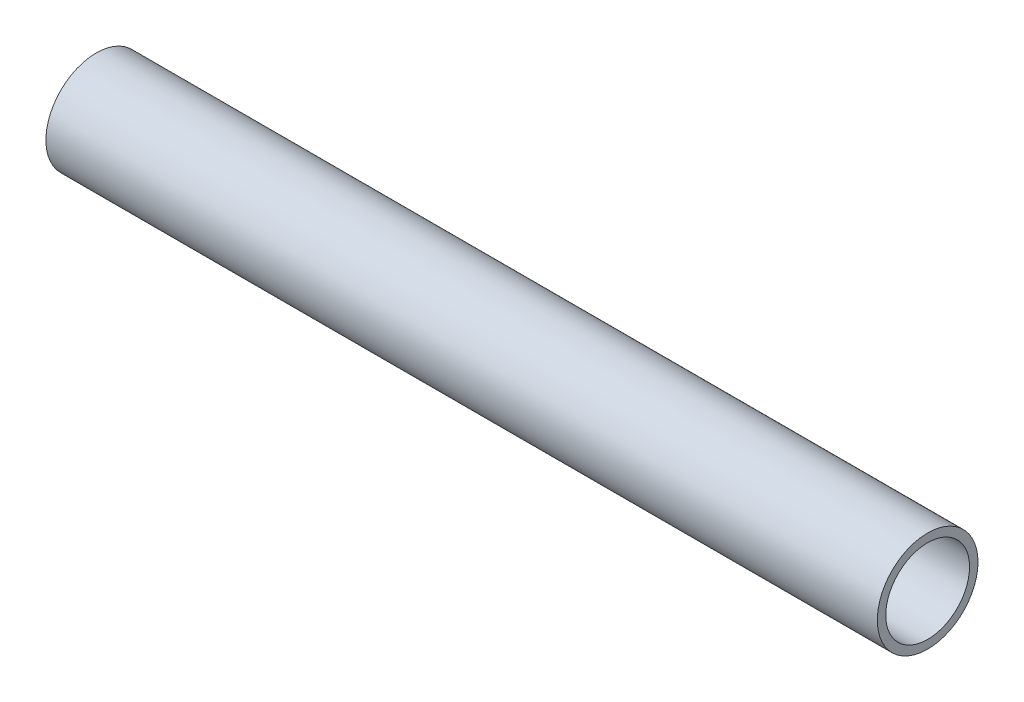
SolidWorks part; units mm, degrees
ref_plane "Front Plane" through (0, 0, 0) normal (0, 0, 1) x (1, 0, 0)
ref_plane "Top Plane" through (0, 0, 0) normal (0, 1, 0) x (1, 0, 0)
ref_plane "Right Plane" through (0, 0, 0) normal (1, 0, 0) x (0, 0, -1)
sketch "Sketch1" plane through (0, 0, 0) normal (0, 0, 1) x (1, 0, 0)
  line L0 (-143.6139, 1471.8597) -> (-38.7684, 1471.8597)
  point P2 (0, 0)
  point P3 (-143.6139, 1471.8597)
  point P5 (0, 0)
  point P6 (-144.5855, 1471.8597)
other "Pipe 0.5 SCH 40(1)"
ref_plane "Plane1" through (-143.6139, 1471.8597, 0) normal (1, 0, 0) x (0, 1, 0)
sketch "Sketch11" plane through (-143.6139, 1471.8597, 0) normal (1, 0, 0) x (0, 1, 0)
  circle A0 centre (0, 0) radius 5.2832
  circle A1 centre (0, 0) radius 6.35
  point P5 (0, 0)
  dimension "D1" = 12.7
  dimension "D2" = 10.5664
